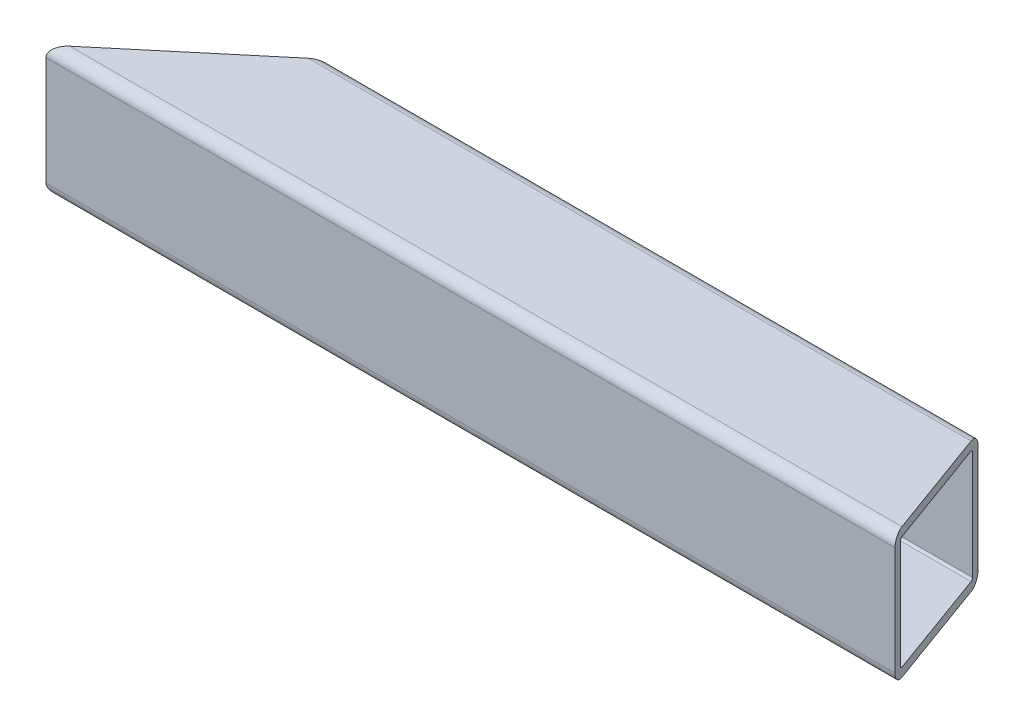
SolidWorks part; units mm, degrees
ref_plane "Front Plane" through (0, 0, 0) normal (0, 0, 1) x (1, 0, 0)
ref_plane "Top Plane" through (0, 0, 0) normal (0, 1, 0) x (1, 0, 0)
ref_plane "Right Plane" through (0, 0, 0) normal (1, 0, 0) x (0, 0, -1)
sketch "Sketch1" plane through (0, 0, 0) normal (1, 0, 0) x (0, 0, -1)
  line L1 (-15.875, 19.05) -> (15.875, 19.05)
  line L2 (-19.05, 15.875) -> (-19.05, -15.875)
  line L3 (-15.875, -19.05) -> (15.875, -19.05)
  line L4 (19.05, 15.875) -> (19.05, -15.875)
  line L5 (-19.05, 19.05) -> (19.05, -19.05) construction
  line L6 (-19.05, -19.05) -> (19.05, 19.05) construction
  arc A0 (-19.05, -15.875) -> (-15.875, -19.05) centre (-15.875, -15.875) ccw
  arc A1 (15.875, -19.05) -> (19.05, -15.875) centre (15.875, -15.875) ccw
  arc A2 (19.05, 15.875) -> (15.875, 19.05) centre (15.875, 15.875) ccw
  arc A3 (-15.875, 19.05) -> (-19.05, 15.875) centre (-15.875, 15.875) ccw
  point P0 (0, 0)
  dimension "D3" = 3.175
  dimension "D1" = 38.1
  dimension "D2" = 38.1
extrude "Extrude-Thin1" add sketch "Sketch1" along normal mid plane 247.9751 thin
sketch "Sketch2" plane through (0, -19.05, 0) normal (0, -1, 0) x (1, 0, 0)
  line L0 (123.9876, 0) -> (-123.9876, 0) construction
  line L1 (123.9876, 15.875) -> (123.9876, -15.875) construction
  line L2 (-123.9876, 15.875) -> (-123.9876, -15.875) construction
  line L3 (73.1876, 15.875) -> (73.1876, -15.875) construction
  line L4 (123.9876, 15.875) -> (-123.9876, 15.875) construction
  line L5 (123.9876, -15.875) -> (-123.9876, -15.875) construction
  line L6 (-85.5624, 15.875) -> (-85.5624, -15.875) construction
  dimension "D1" = 209.55
  dimension "D2" = 50.8
sketch "Sketch3" plane through (0, 19.05, 0) normal (0, 1, 0) x (1, 0, 0)
  line L0 (123.9876, -19.05) -> (110.1203, 19.05)
  line L1 (123.9876, 19.05) -> (-123.9876, 19.05) construction
  line L3 (123.9876, 15.875) -> (123.9876, -15.875) construction
  dimension "D1" = 20
extrude "Cut-Extrude1" cut sketch "Sketch3" against normal through all and the other way through all flip side to cut
sketch "Sketch4" plane through (0, 19.05, 0) normal (0, 1, 0) x (1, 0, 0)
  line L0 (-123.9876, -19.05) -> (-78.5817, 19.05)
  line L1 (110.1203, 19.05) -> (-123.9876, 19.05) construction
  line L2 (-123.9876, 15.875) -> (-123.9876, -15.875) construction
  dimension "D1" = 50
extrude "Cut-Extrude2" cut sketch "Sketch4" against normal through all and the other way through all
